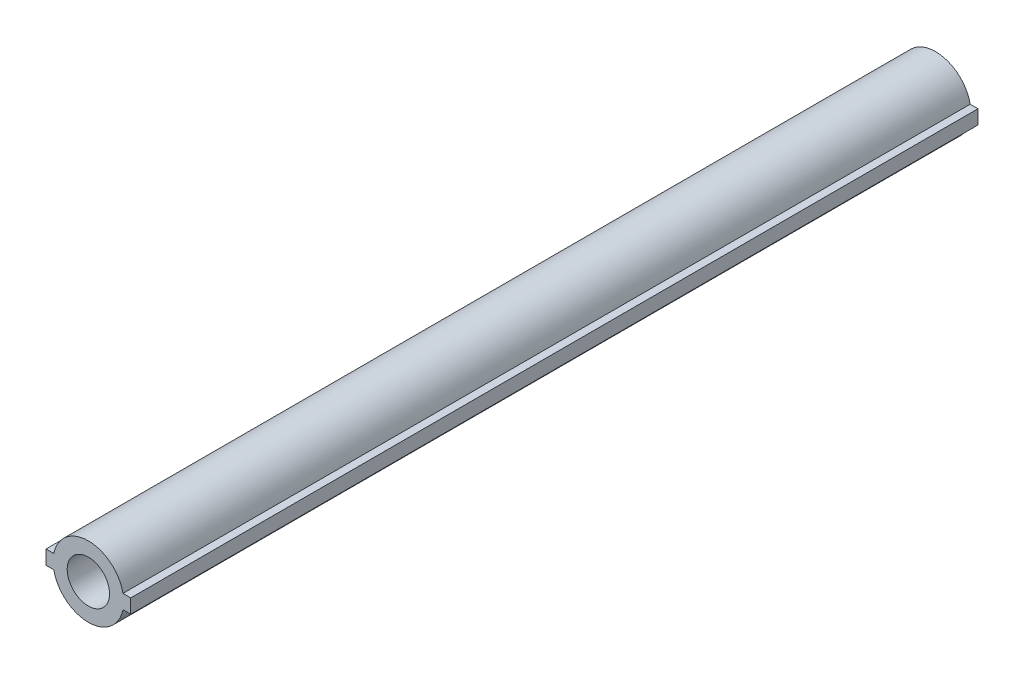
SolidWorks part; units mm, degrees
ref_plane "Front Plane" through (0, 0, 0) normal (0, 0, 1) x (1, 0, 0)
ref_plane "Top Plane" through (0, 0, 0) normal (0, 1, 0) x (1, 0, 0)
ref_plane "Right Plane" through (0, 0, 0) normal (1, 0, 0) x (0, 0, -1)
sketch "Sketch1" plane through (0, 0, 0) normal (0, 0, 1) x (1, 0, 0)
  circle A0 centre (0, 0) radius 750
  dimension "D1" = 1500
extrude "Boss-Extrude1" add sketch "Sketch1" along normal blind 18000
sketch "Sketch2" plane through (0, 0, 18000) normal (0, 0, 1) x (1, 0, 0)
  line L1 (-900, -150) -> (900, -150)
  line L2 (-900, -150) -> (-900, 150)
  line L3 (-900, 150) -> (900, 150)
  line L4 (900, -150) -> (900, 150)
  line L5 (-900, -150) -> (900, 150) construction
  line L6 (-900, 150) -> (900, -150) construction
  point P0 (0, 0)
  dimension "D1" = 300
  dimension "D2" = 1800
extrude "Boss-Extrude2" add sketch "Sketch2" against normal blind 18000
sketch "Sketch3" plane through (0, 0, 0) normal (0, 0, -1) x (-1, 0, 0)
  circle A0 centre (0, 0) radius 450
  dimension "D1" = 900
extrude "Cut-Extrude1" cut sketch "Sketch3" along normal blind 12000 from offset 18000
